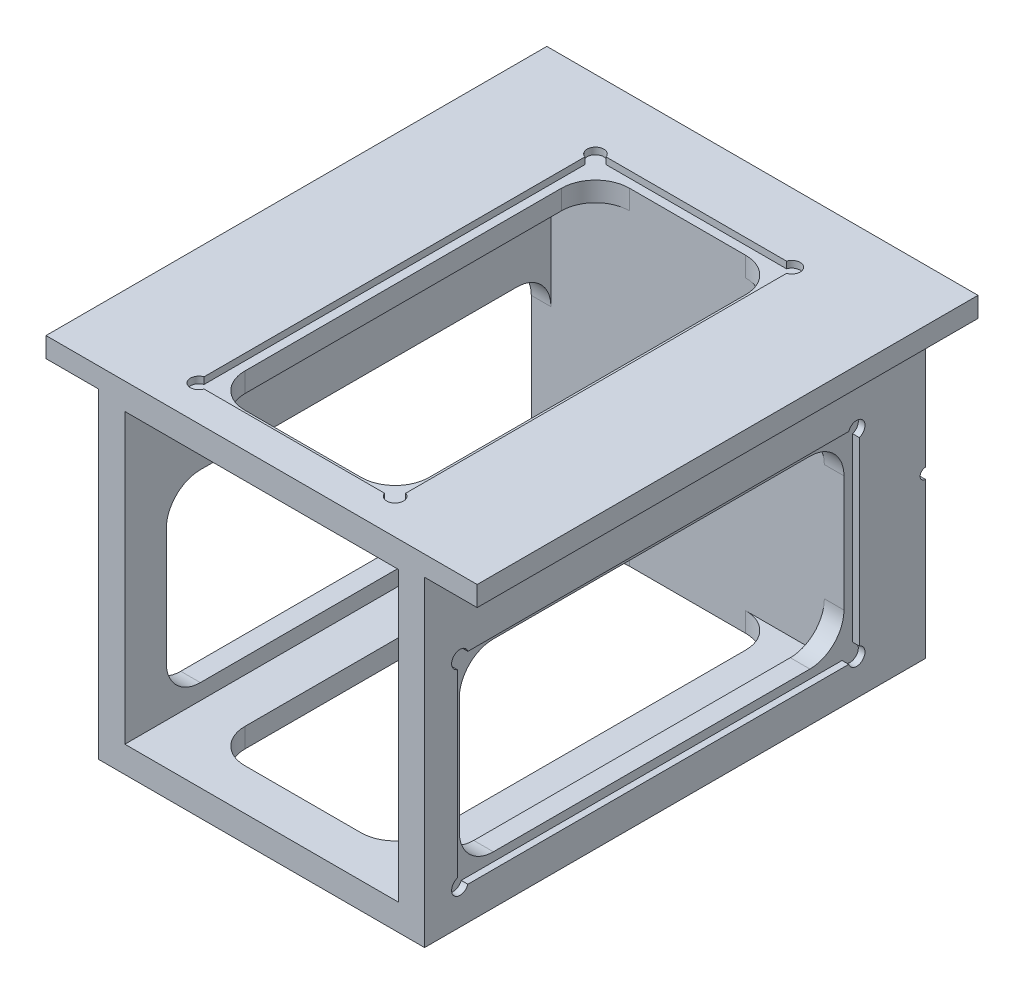
SolidWorks part; units mm, degrees
ref_plane "Front Plane" through (0, 0, 0) normal (0, 0, 1) x (1, 0, 0)
ref_plane "Top Plane" through (0, 0, 0) normal (0, 1, 0) x (1, 0, 0)
ref_plane "Right Plane" through (0, 0, 0) normal (1, 0, 0) x (0, 0, -1)
sketch "Sketch1" plane through (0, 0, 0) normal (0, 0, 1) x (1, 0, 0)
  line L0 (-41, 29.31) -> (41, 29.31)
  line L2 (-31, 25.5) -> (-31, -35.5)
  line L3 (-31, -35.5) -> (31, -35.5)
  line L4 (31, 25.5) -> (31, -35.5)
  line L7 (-41, 25.5) -> (-31, 25.5)
  line L8 (-41, 29.31) -> (-41, 25.5)
  line L9 (31, 25.5) -> (41, 25.5)
  line L10 (41, 25.5) -> (41, 29.31)
  dimension "D1" = 10
  dimension "D2" = 10
  dimension "D3" = 61
  dimension "D4" = 3.81
  dimension "D5" = 35.5
  dimension "D6" = 62
  dimension "D7" = 31
extrude "Boss-Extrude1" add sketch "Sketch1" along normal blind 88.9
sketch "Sketch6" plane through (-31, 0, 0) normal (-1, 0, 0) x (0, 0, 1)
  line L0 (88.9, 25.5) -> (0, 25.5) construction
  line L1 (88.9, -35.5) -> (0, -35.5) construction
  line L38 (14.351, 7.526) -> (74.549, 7.526)
  line L45 (81.026, -21.049) -> (81.026, 1.049)
  line L46 (14.351, -27.526) -> (74.549, -27.526)
  line L47 (7.874, -21.049) -> (7.874, 1.049)
  arc A20 (74.549, 7.526) -> (81.026, 1.049) centre (74.549, 1.049) cw
  arc A21 (81.026, -21.049) -> (74.549, -27.526) centre (74.549, -21.049) cw
  arc A22 (14.351, -27.526) -> (7.874, -21.049) centre (14.351, -21.049) cw
  arc A23 (14.351, 7.526) -> (7.874, 1.049) centre (14.351, 1.049) ccw
  point P14 (81.026, -10)
  dimension "D1" = 6.477
  dimension "D2" = 35.5
extrude "Cut-Extrude5" cut sketch "Sketch6" against normal through all
sketch "Sketch7" plane through (0, -35.5, 0) normal (0, -1, 0) x (0, 0, 1)
  line L38 (14.351, 17.526) -> (74.549, 17.526)
  line L45 (81.026, -11.049) -> (81.026, 11.049)
  line L46 (14.351, -17.526) -> (74.549, -17.526)
  line L47 (7.874, -11.049) -> (7.874, 11.049)
  arc A20 (74.549, 17.526) -> (81.026, 11.049) centre (74.549, 11.049) cw
  arc A21 (81.026, -11.049) -> (74.549, -17.526) centre (74.549, -11.049) cw
  arc A22 (14.351, -17.526) -> (7.874, -11.049) centre (14.351, -11.049) cw
  arc A23 (14.351, 17.526) -> (7.874, 11.049) centre (14.351, 11.049) ccw
  dimension "D1" = 6.477
extrude "Cut-Extrude6" cut sketch "Sketch7" against normal through all
sketch "Sketch8" plane through (0, 0, 88.9) normal (0, 0, 1) x (1, 0, 0)
  line L21 (-26, 24.31) -> (-26, -30.5)
  line L22 (-31, 25.5) -> (-31, -35.5) construction
  line L23 (-26, -30.5) -> (26, -30.5)
  line L24 (-31, -35.5) -> (31, -35.5) construction
  line L26 (26, -30.5) -> (26, 24.31)
  line L27 (31, -35.5) -> (31, 25.5) construction
  line L28 (26, 24.31) -> (-26, 24.31)
  line L29 (41, 29.31) -> (-41, 29.31) construction
  point P0 (0, 0)
  point P7 (17.526, 7.526)
  dimension "D1" = 5
  dimension "D2" = 5
  dimension "D3" = 5
  dimension "D4" = 5
extrude "Cut-Extrude7" cut sketch "Sketch8" against normal blind 15.875
sketch "Sketch12" plane through (0, 0, 88.9) normal (0, 0, 1) x (1, 0, 0)
  line L5 (-26, 24.31) -> (26, 24.31)
  line L6 (-26, 24.31) -> (-26, -30.5)
  line L7 (-26, -30.5) -> (26, -30.5)
  line L8 (26, 24.31) -> (26, -30.5)
extrude "Cut-Extrude11" cut sketch "Sketch12" against normal blind 63.5
sketch "Sketch18" plane through (0, 0, 88.9) normal (0, 0, 1) x (1, 0, 0)
  line L6 (-26, 24.31) -> (26, 24.31)
  line L8 (-26, 24.31) -> (-26, -30.5)
  line L9 (-26, -30.5) -> (26, -30.5)
  line L10 (26, 24.31) -> (26, -30.5)
extrude "Cut-Extrude14" cut sketch "Sketch18" against normal up to surface (81.026 mm away) up to face at (0, -7.6983, 7.874)
sketch "Sketch19" plane through (0, 0, 0) normal (0, 0, -1) x (-1, 0, 0)
  line L0 (31, 25.5) -> (41, 25.5)
  line L1 (-41, 29.31) -> (41, 29.31)
  line L2 (-41, 29.31) -> (-41, 25.5)
  line L3 (-41, 25.5) -> (-31, 25.5)
  line L4 (41, 29.31) -> (41, 25.5)
  line L5 (31, -35.5) -> (-31, -35.5)
  line L6 (31, -35.5) -> (31, 25.5)
  line L8 (-31, -35.5) -> (-31, 25.5)
extrude "Boss-Extrude2" add sketch "Sketch19" along normal blind 6.35
sketch "Sketch20" plane through (0, 0, -6.35) normal (0, 0, -1) x (-1, 0, 0)
  circle A1 centre (0, -4.8446) radius 2.5527
  dimension "D1" = 5.1054
extrude "Cut-Extrude15" cut sketch "Sketch20" against normal blind 9.525
sketch "Sketch21" plane through (31, 0, 0) normal (1, 0, 0) x (0, 0, -1)
  line L0 (6.35, 25.5) -> (6.35, -35.5) construction
  line L1 (6.35, -4) -> (6.35, -6)
  arc A0 (6.35, -4) -> (6.35, -6) centre (6.35, -5) ccw
  dimension "D1" = 2
extrude "Cut-Extrude16" cut sketch "Sketch21" against normal through all
sketch "Sketch22" plane through (0, -35.5, 0) normal (0, -1, 0) x (-1, 0, 0)
  line L0 (17.526, -74.549) -> (17.526, -14.351) construction
  line L5 (-17.165, -6.223) -> (17.165, -6.223)
  line L6 (-19.177, -8.235) -> (-19.177, -80.665)
  line L7 (-17.165, -82.677) -> (17.165, -82.677)
  line L8 (19.177, -8.235) -> (19.177, -80.665)
  line L9 (-19.177, -6.223) -> (19.177, -82.677) construction
  line L10 (-19.177, -82.677) -> (19.177, -6.223) construction
  line L22 (-29.0769, -44.45) -> (33.4177, -44.45) construction
  arc A5 (-17.165, -6.223) -> (-19.177, -8.235) centre (-18.669, -6.731) ccw
  arc A18 (19.177, -8.235) -> (17.165, -6.223) centre (18.669, -6.731) ccw
  arc A19 (-17.165, -82.677) -> (-19.177, -80.665) centre (-18.669, -82.169) cw
  arc A20 (19.177, -80.665) -> (17.165, -82.677) centre (18.669, -82.169) cw
  point P0 (0, -44.45)
  point P7 (17.526, -44.45)
  dimension "D5" = 3.175
  dimension "D1" = 76.454
  dimension "D2" = 38.354
  dimension "D3" = 0
  dimension "D4" = 0
extrude "Cut-Extrude17" cut sketch "Sketch22" against normal blind 1.27
sketch "Sketch23" plane through (-31, 0, 0) normal (-1, 0, 0) x (0, 1, 0)
  line L0 (-21.049, -81.026) -> (1.049, -81.026) construction
  line L5 (-27.165, -6.223) -> (7.165, -6.223)
  line L6 (-29.177, -8.235) -> (-29.177, -80.665)
  line L7 (-27.165, -82.677) -> (7.165, -82.677)
  line L8 (9.177, -8.235) -> (9.177, -80.665)
  line L9 (-29.177, -6.223) -> (9.177, -82.677) construction
  line L10 (-29.177, -82.677) -> (9.177, -6.223) construction
  line L11 (7.526, -74.549) -> (7.526, -14.351) construction
  arc A5 (-27.165, -6.223) -> (-29.177, -8.235) centre (-28.669, -6.731) ccw
  arc A6 (9.177, -8.235) -> (7.165, -6.223) centre (8.669, -6.731) ccw
  arc A7 (7.165, -82.677) -> (9.177, -80.665) centre (8.669, -82.169) ccw
  arc A8 (-29.177, -80.665) -> (-27.165, -82.677) centre (-28.669, -82.169) ccw
  point P0 (-10, -44.45)
  point P7 (-10, -81.026)
  point P10 (7.526, -44.45)
  dimension "D6" = 3.175
  dimension "D1" = 38.354
  dimension "D2" = 76.454
  dimension "D3" = 0
  dimension "D4" = 0
extrude "Cut-Extrude18" cut sketch "Sketch23" against normal blind 1.27
sketch "Sketch24" plane through (31, 0, 0) normal (1, 0, 0) x (0, -1, 0)
  line L5 (-7.165, -6.223) -> (27.165, -6.223)
  line L6 (-9.177, -8.235) -> (-9.177, -80.665)
  line L7 (-7.165, -82.677) -> (27.165, -82.677)
  line L8 (29.177, -8.235) -> (29.177, -80.665)
  line L9 (-9.177, -6.223) -> (29.177, -82.677) construction
  line L10 (-9.177, -82.677) -> (29.177, -6.223) construction
  line L11 (27.526, -14.351) -> (27.526, -74.549) construction
  line L12 (-1.049, -7.874) -> (21.049, -7.874) construction
  arc A0 (-7.165, -6.223) -> (-9.177, -8.235) centre (-8.669, -6.731) ccw
  arc A1 (29.177, -8.235) -> (27.165, -6.223) centre (28.669, -6.731) ccw
  arc A2 (27.165, -82.677) -> (29.177, -80.665) centre (28.669, -82.169) ccw
  arc A3 (-9.177, -80.665) -> (-7.165, -82.677) centre (-8.669, -82.169) ccw
  point P0 (10, -44.45)
  point P7 (27.526, -44.45)
  point P10 (10, -7.874)
  dimension "D6" = 3.175
  dimension "D1" = 76.454
  dimension "D2" = 38.354
  dimension "D3" = 0
  dimension "D4" = 0
extrude "Cut-Extrude19" cut sketch "Sketch24" against normal blind 1.27
sketch "Sketch25" plane through (0, 29.31, 0) normal (0, 1, 0) x (1, 0, 0)
  line L0 (17.526, -14.351) -> (17.526, -74.549) construction
  line L5 (-17.165, -6.223) -> (17.165, -6.223)
  line L6 (-19.177, -8.235) -> (-19.177, -80.665)
  line L7 (-17.165, -82.677) -> (17.165, -82.677)
  line L8 (19.177, -8.235) -> (19.177, -80.665)
  line L9 (-19.177, -6.223) -> (19.177, -82.677) construction
  line L10 (-19.177, -82.677) -> (19.177, -6.223) construction
  line L11 (-11.049, -7.874) -> (11.049, -7.874) construction
  arc A5 (-17.165, -6.223) -> (-19.177, -8.235) centre (-18.669, -6.731) ccw
  arc A6 (19.177, -8.235) -> (17.165, -6.223) centre (18.669, -6.731) ccw
  arc A7 (17.165, -82.677) -> (19.177, -80.665) centre (18.669, -82.169) ccw
  arc A8 (-19.177, -80.665) -> (-17.165, -82.677) centre (-18.669, -82.169) ccw
  point P0 (0, -44.45)
  point P7 (17.526, -44.45)
  point P10 (0, -7.874)
  dimension "D6" = 3.175
  dimension "D1" = 76.454
  dimension "D2" = 38.354
  dimension "D3" = 0
  dimension "D4" = 0
extrude "Cut-Extrude20" cut sketch "Sketch25" against normal blind 1.27
